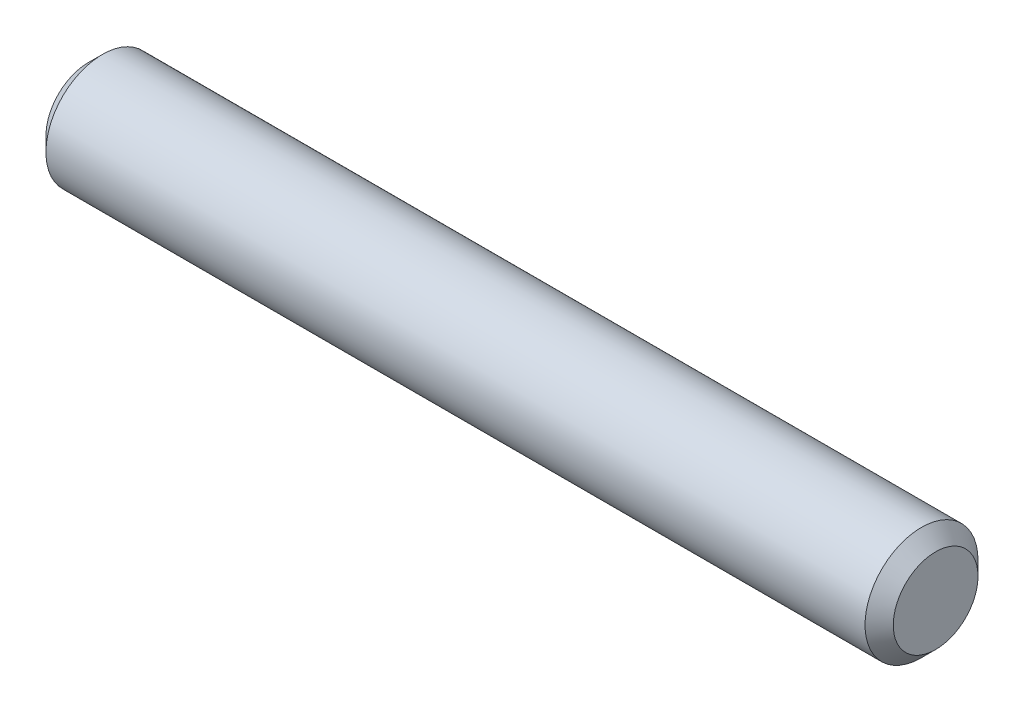
SolidWorks part; units mm, degrees
ref_plane "Front Plane" through (0, 0, 0) normal (0, 0, 1) x (1, 0, 0)
ref_plane "Top Plane" through (0, 0, 0) normal (0, 1, 0) x (1, 0, 0)
ref_plane "Right Plane" through (0, 0, 0) normal (1, 0, 0) x (0, 0, -1)
sketch "Sketch1" plane through (0, 0, 0) normal (1, 0, 0) x (0, 0, -1)
  circle A0 centre (0, 0) radius 2
  dimension "D1" = 4
extrude "Boss-Extrude1" add sketch "Sketch1" along normal mid plane 30
chamfer "Chamfer1" distance 0.5 angle 45 2 edges at (15, 0, -2) (-15, 0, -2)
